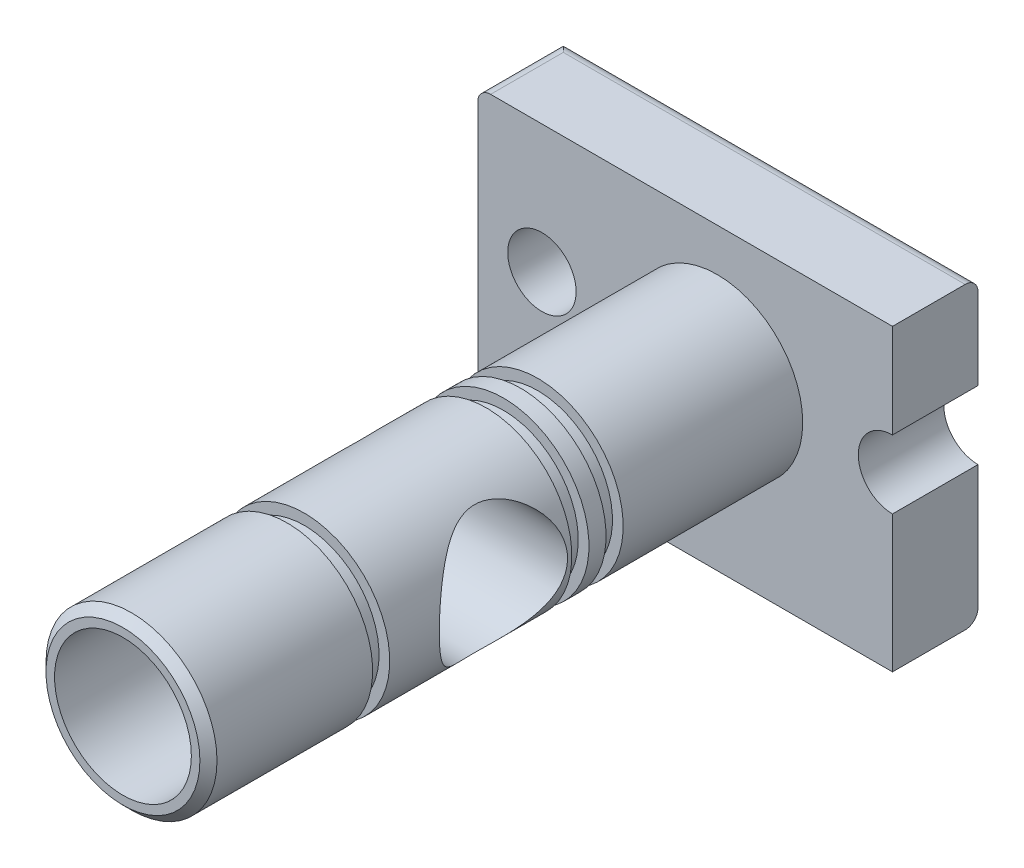
SolidWorks part; units mm, degrees
ref_plane "Front Plane" through (0, 0, 0) normal (0, 0, 1) x (1, 0, 0)
ref_plane "Top Plane" through (0, 0, 0) normal (0, 1, 0) x (1, 0, 0)
ref_plane "Right Plane" through (0, 0, 0) normal (1, 0, 0) x (0, 0, -1)
sketch "Sketch1" plane through (0, 0, 0) normal (0, 0, 1) x (1, 0, 0)
  line L1 (-56, 30) -> (41, 30)
  line L3 (-56, -40) -> (41, -40)
  line L4 (41, 30) -> (41, 8)
  line L5 (41, -8) -> (41, -40)
  line L6 (-56, 30) -> (-56, -40)
  arc A1 (41, 8) -> (41, -8) centre (41, 0) ccw
  circle A2 centre (-41, 0) radius 8
  dimension "D5" = 56
  dimension "D6" = 16
  dimension "D1" = 70
  dimension "D2" = 97
  dimension "D3" = 15
  dimension "D4" = 40
extrude "Boss-Extrude1" add sketch "Sketch1" along normal blind 20
sketch "Sketch2" plane through (0, 0, 20) normal (0, 0, 1) x (1, 0, 0)
  circle A0 centre (0, 0) radius 20
  dimension "D1" = 40
extrude "Boss-Extrude2" add sketch "Sketch2" along normal blind 139
sketch "Sketch3" plane through (0, 0, 0) normal (1, 0, 0) x (0, 0, -1)
  line L0 (-20, 8) -> (-20, 30) construction
  circle A0 centre (-90, 0) radius 15
  point P4 (0, 0)
  dimension "D1" = 30
  dimension "D2" = 70
extrude "Cut-Extrude1" cut sketch "Sketch3" against normal through all both and the other way through all
sketch "Sketch4" plane through (0, 0, 0) normal (1, 0, 0) x (0, 0, -1)
  line L0 (-20, 20) -> (-159, 20) construction
  line L1 (-66, 20) -> (-62, 20)
  line L2 (-66, 20) -> (-66, 17.5)
  line L3 (-66, 17.5) -> (-62, 17.5)
  line L4 (-62, 20) -> (-62, 17.5)
  line L5 (-20, 8) -> (-20, 30) construction
  line L6 (-74, 20) -> (-70, 20)
  line L7 (-74, 20) -> (-74, 17.5)
  line L8 (-74, 17.5) -> (-70, 17.5)
  line L9 (-70, 20) -> (-70, 17.5)
  line L10 (-120.6, 20) -> (-116.6, 20)
  line L11 (-120.6, 20) -> (-120.6, 17.5)
  line L12 (-120.6, 17.5) -> (-116.6, 17.5)
  line L13 (-116.6, 20) -> (-116.6, 17.5)
  line L14 (0, 0) -> (-203.4126, 0) construction
  dimension "D1" = 2.5
  dimension "D2" = 4
  dimension "D3" = 4
  dimension "D4" = 4
  dimension "D5" = 4
  dimension "D6" = 42
  dimension "D7" = 42.6
revolve "Cut-Revolve1" cut sketch "Sketch4" angle 360 about L14
sketch "Sketch5" plane through (0, 0, 159) normal (0, 0, 1) x (1, 0, 0)
  circle A0 centre (0, 0) radius 16
  dimension "D1" = 32
extrude "Cut-Extrude2" cut sketch "Sketch5" against normal blind 45.4
sketch "Sketch6" plane through (0, 0, 113.6) normal (0, 0, 1) x (1, 0, 0)
  circle A0 centre (0, 0) radius 9.5
  dimension "D1" = 19
extrude "Cut-Extrude3" cut sketch "Sketch6" against normal blind 12
chamfer "Chamfer1" distance 2 1 edges at (20, 0, 159)
fillet "Fillet1" radius 3 4 edges at (-7.5, -40, 0) (-7.5, 30, 0) (-56, -40, 10) (-56, 30, 10)
